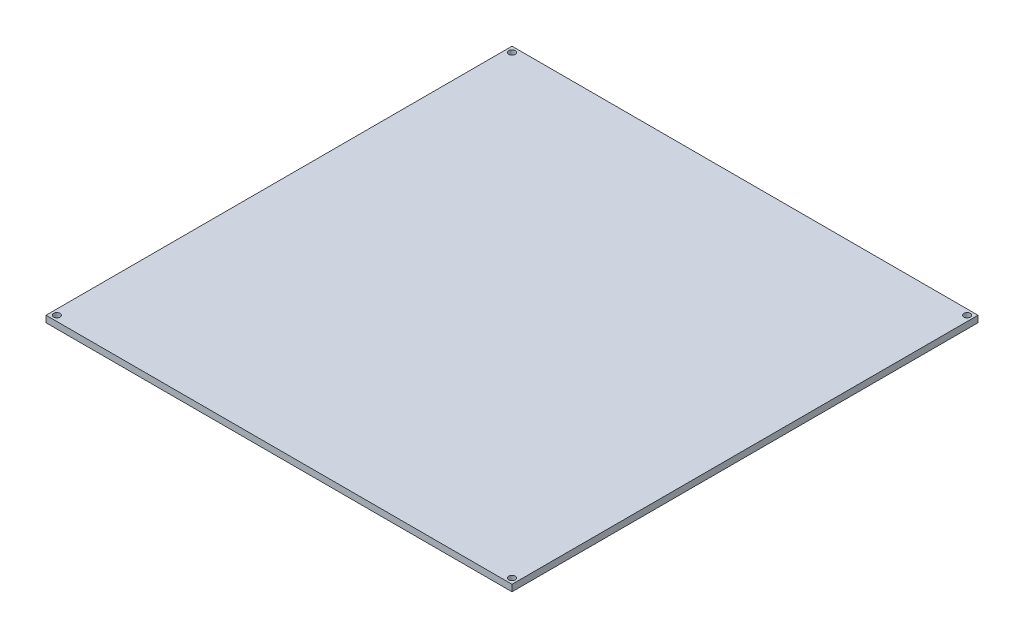
SolidWorks part; units mm, degrees
ref_plane "Alzado" through (0, 0, 0) normal (0, 0, 1) x (1, 0, 0)
ref_plane "Planta" through (0, 0, 0) normal (0, 1, 0) x (1, 0, 0)
ref_plane "Vista lateral" through (0, 0, 0) normal (1, 0, 0) x (0, 0, -1)
sketch "Croquis1" plane through (0, 0, 0) normal (0, 1, 0) x (1, 0, 0)
  line L1 (0, 0) -> (214, 0)
  line L2 (0, 0) -> (0, 214)
  line L3 (0, 214) -> (214, 214)
  line L4 (214, 0) -> (214, 214)
  dimension "D1" = 214
  dimension "D2" = 214
extrude "Saliente-Extruir1" add sketch "Croquis1" along normal blind 3
sketch "Croquis2" plane through (0, 3, 0) normal (0, 1, 0) x (1, 0, 0)
  line L0 (214, 214) -> (0, 214) construction
  line L2 (0, 214) -> (0, 0) construction
  circle A0 centre (2.5, 211.5) radius 1.5
  circle A1 centre (2.5, 2.5) radius 1.5
  circle A2 centre (211.5, 2.5) radius 1.5
  circle A3 centre (211.5, 211.5) radius 1.5
  point P8 (0, 0)
  point P9 (0, 0)
  point P10 (0, 0)
  point P11 (0, 0)
  point P16 (0, 207.6688)
  dimension "D1" = 3
  dimension "D2" = 3
  dimension "D3" = 3
  dimension "D4" = 3
  dimension "D5" = 209
  dimension "D6" = 209
  dimension "D7" = 2.5
  dimension "D8" = 2.5
extrude "Cortar-Extruir1" cut sketch "Croquis2" against normal blind 3
